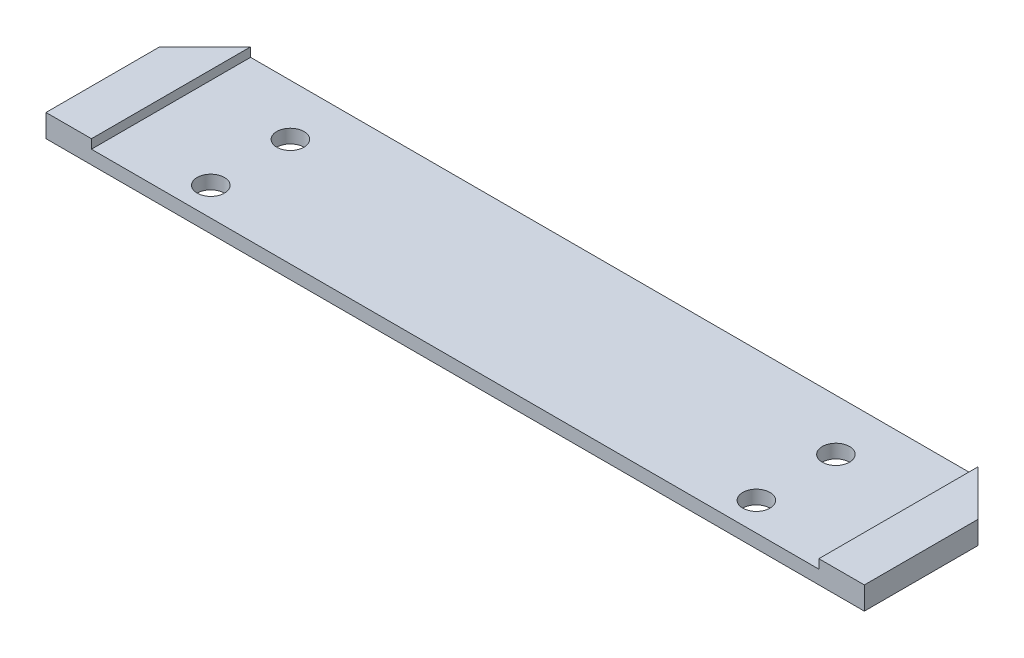
SolidWorks part; units mm, degrees
material "6061 Alloy"
ref_plane "Front Plane" through (0, 0, 0) normal (0, 0, 1) x (1, 0, 0)
ref_plane "Top Plane" through (0, 0, 0) normal (0, 1, 0) x (1, 0, 0)
ref_plane "Right Plane" through (0, 0, 0) normal (1, 0, 0) x (0, 0, -1)
sketch "Sketch1" plane through (0, 0, 0) normal (0, 1, 0) x (1, 0, 0)
  line L1 (-90, -17.5) -> (90, -17.5)
  line L2 (-90, -17.5) -> (-90, 17.5)
  line L3 (-90, 17.5) -> (90, 17.5)
  line L4 (90, -17.5) -> (90, 17.5)
  line L5 (-90, -17.5) -> (90, 17.5) construction
  line L6 (-90, 17.5) -> (90, -17.5) construction
  point P0 (0, 0)
  dimension "D1" = 35
  dimension "D2" = 180
extrude "Boss-Extrude1" add sketch "Sketch1" along normal blind 5
sketch "Sketch2" plane through (0, 5, 0) normal (0, 1, 0) x (1, 0, 0)
  line L1 (-60, -11.25) -> (60, -11.25)
  line L2 (-60, -11.25) -> (-60, 6.25)
  line L3 (-60, 6.25) -> (60, 6.25)
  line L4 (60, -11.25) -> (60, 6.25)
  line L5 (-60, -11.25) -> (60, 6.25) construction
  line L6 (-60, 6.25) -> (60, -11.25) construction
  point P0 (0, -2.5)
  dimension "D1" = 2.5
  dimension "D2" = 17.5
  dimension "D3" = 120
hole_wizard "Ø6.0mm Dowel Hole1" positions "3DSketch1" profile "Sketch3" hole size "Ø6.0" standard "ISO" end condition through all
sketch3d "3DSketch1"
  point P0 (-60, 5, -6.25)
  point P3 (-60, 5, 11.25)
  point P6 (60, 5, -6.25)
  point P9 (60, 5, 11.25)
sketch "Sketch3" plane through (-60, 5, -6.25) normal (1, 0, 0) x (0, 0, 1)
  line L0 (0, 0) -> (0, 5)
  line L1 (0, 5) -> (3, 5)
  line L2 (3, 5) -> (3, 0)
  line L5 (3, 0) -> (0, 0)
  line L11 (0, -6.35) -> (0, 107.95) construction
  dimension "Thru Hole Dia." = 6
  dimension "Thru Hole Depth" = 5
sketch "Sketch4" plane through (0, 5, 0) normal (0, 1, 0) x (1, 0, 0)
  line L0 (90, 17.5) -> (-90, 17.5) construction
  line L2 (-90, 17.5) -> (-90, -17.5) construction
  line L3 (-90, -17.5) -> (90, -17.5) construction
  line L4 (90, 17.5) -> (90, -17.5) construction
  line L5 (-90, 17.5) -> (90, -17.5) construction
  line L6 (-90, -17.5) -> (90, 17.5) construction
  line L11 (-80, 17.5) -> (80, 17.5)
  line L12 (-80, 17.5) -> (-80, -17.5)
  line L13 (-80, -17.5) -> (80, -17.5)
  line L14 (80, 17.5) -> (80, -17.5)
  line L19 (-80, 17.5) -> (80, -17.5) construction
  line L20 (-80, -17.5) -> (80, 17.5) construction
  point P4 (0, 0)
  point P11 (0, 0)
  point P14 (0, 0)
  point P15 (0, 0)
  dimension "D1" = 10
  dimension "D2" = 160
extrude "Cut-Extrude1" cut sketch "Sketch4" against normal blind 2
chamfer "Chamfer1" distance 10 angle 45 2 edges at (90, 2.5, -17.5) (-90, 2.5, -17.5)
